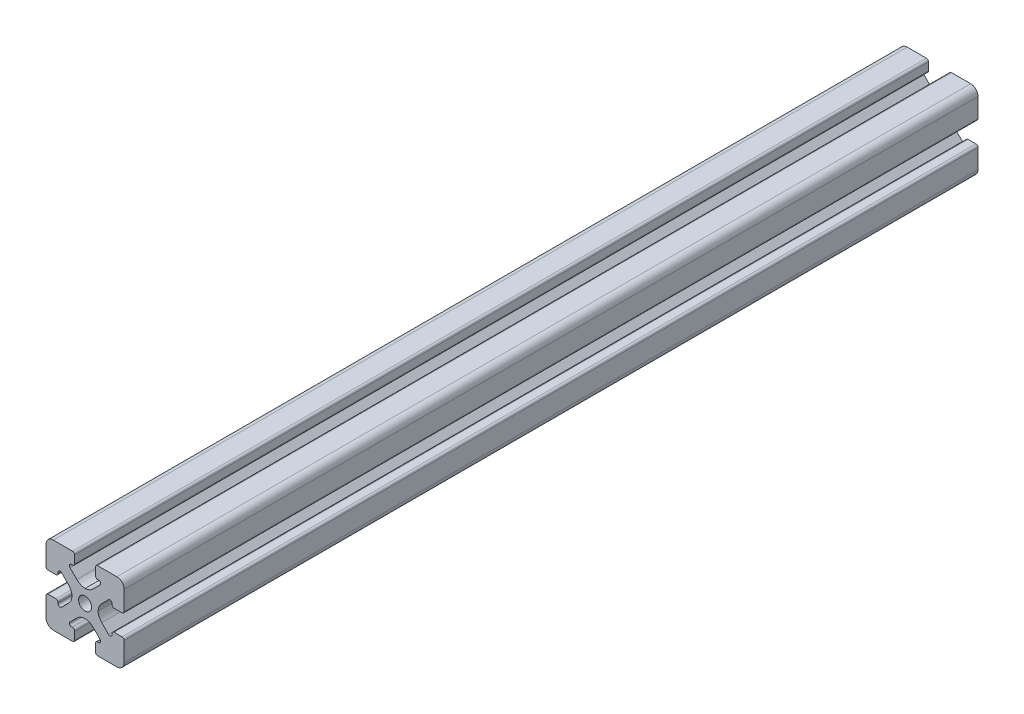
SolidWorks part; units mm, degrees
ref_plane "Front Plane" through (0, 0, 0) normal (0, 0, 1) x (1, 0, 0)
ref_plane "Top Plane" through (0, 0, 0) normal (0, 1, 0) x (1, 0, 0)
ref_plane "Right Plane" through (0, 0, 0) normal (1, 0, 0) x (0, 0, -1)
sketch "Sketch2" plane through (0, 0, 0) normal (0, 0, 1) x (1, 0, 0)
  line L0 (0, 7.5) -> (0, -7.5) construction
  line L1 (-7.5, 0) -> (7.5, 0) construction
  line L2 (2, -7.5) -> (7.5, -7.5)
  line L3 (7.5, -7.5) -> (7.5, -2)
  line L4 (2, -7.5) -> (2, -5.1953)
  line L5 (2, -5.1953) -> (3.5657, -5.1953)
  line L6 (3.5657, -5.1953) -> (0.8704, -2.5)
  line L7 (0, 0) -> (7.5, -7.5) construction
  line L8 (7.5, -2) -> (5.1953, -2)
  line L9 (5.1953, -2) -> (5.1953, -3.5657)
  line L10 (5.1953, -3.5657) -> (2.5, -0.8704)
  line L11 (3.8477, -2.218) -> (2.218, -3.8477) construction
  circle A0 centre (0, 0) radius 1.25
  arc A1 (2.6, -5.1953) -> (2.8828, -4.5125) centre (2.6, -4.7953) ccw construction
  point P8 (0, -2.5)
  point P16 (3.0328, -3.0328)
  dimension "Center Hole Diameter" = 2.5
  dimension "D3" = 0.4
  dimension "Rail Height" = 15
  dimension "Rail Width" = 15
  dimension "T-Slot Width" = 4
  dimension "Slot Depth" = 5
  dimension "Slot Inner Width" = 6
sketch "Sketch3" plane through (0, 0, 0) normal (1, 0, 0) x (0, 0, -1)
  line L0 (-82, -7.5) -> (82, -7.5) construction
  line L1 (-56.6, 0) -> (56.6, 0) construction
  line L2 (0, 7.5) -> (0, -7.5) construction
  line L3 (0, 7.5) -> (0, -7.5) construction
  point P6 (-56.6, 0)
  point P8 (56.6, 0)
  dimension "Length" = 164
  dimension "D1" = 25.4
sketch "Sketch4" plane through (0, 0, 0) normal (0, 0, 1) x (1, 0, 0)
  line L0 (2.4, -7.5) -> (6.1, -7.5)
  line L1 (2, -7.5) -> (7.5, -7.5) construction
  line L2 (2, -7.5) -> (2, -5.1953) construction
  line L3 (2, -5.1953) -> (3.5657, -5.1953) construction
  line L4 (2, -5.5953) -> (2, -7.1)
  line L5 (2.4, -5.1953) -> (2.6, -5.1953)
  line L6 (0, -2.5) -> (-0.1238, -2.5)
  line L7 (3.5657, -5.1953) -> (0.8704, -2.5) construction
  line L8 (1.5733, -3.2029) -> (2.8828, -4.5125)
  line L9 (7.5, -7.5) -> (7.5, -2) construction
  line L10 (5.1953, -3.5657) -> (2.5, -0.8704) construction
  line L11 (5.1953, -2) -> (5.1953, -3.5657) construction
  line L12 (5.1953, -2.6) -> (5.1953, -2.4)
  line L13 (7.5, -2) -> (5.1953, -2) construction
  line L14 (5.5953, -2) -> (7.1, -2)
  line L15 (7.5, -2.4) -> (7.5, -6.1)
  line L16 (4.5125, -2.8828) -> (3.2029, -1.5733)
  line L17 (2.5, 0) -> (2.5, 0.1238)
  line L18 (-7.5, 0) -> (7.5, 0) construction
  line L19 (0, -2.5) -> (0, -1.25)
  line L20 (0, 7.5) -> (0, -7.5) construction
  line L21 (2.5, 0) -> (1.25, 0)
  arc A0 (2, -7.1) -> (2.4, -7.5) centre (2.4, -7.1) ccw
  arc A1 (2.6, -5.1953) -> (2.8828, -4.5125) centre (2.6, -4.7953) ccw construction
  arc A2 (2, -5.5953) -> (2.4, -5.1953) centre (2.4, -5.5953) cw
  arc A3 (2.6, -5.1953) -> (2.8828, -4.5125) centre (2.6, -4.7953) ccw
  arc A4 (-0.1238, -2.5) -> (1.5733, -3.2029) centre (-0.1238, -4.9) cw
  arc A5 (6.1, -7.5) -> (7.5, -6.1) centre (6.1, -6.1) ccw
  arc A6 (4.5125, -2.8828) -> (5.1953, -2.6) centre (4.7953, -2.6) ccw
  arc A7 (5.1953, -2.4) -> (5.5953, -2) centre (5.5953, -2.4) cw
  arc A8 (7.1, -2) -> (7.5, -2.4) centre (7.1, -2.4) cw
  arc A9 (3.2029, -1.5733) -> (2.5, 0.1238) centre (4.9, 0.1238) cw
  circle A10 centre (0, 0) radius 1.25 construction
  arc A11 (0, -1.25) -> (1.25, 0) centre (0, 0) ccw
  dimension "D1" = 1.4
  dimension "D2" = 2.4
extrude "Boss-Extrude1" add sketch "Sketch4" along normal mid plane 164
mirror "Mirror1" about plane through (0, 0, 0) normal (1, 0, 0) of bodies 134
mirror "Mirror2" about plane through (0, 0, 0) normal (0, 1, 0) of bodies 135
equation "\"D3@Sketch2\"=\"T-Slot Width@Sketch2\"*0.1"
equation "\"D1@Sketch4\"=\"D3@Sketch2\"*3.5"
equation "\"D2@Sketch4\"=\"D3@Sketch2\"*6"
equation "\"D1@Boss-Extrude1\"=\"Length@Sketch3\""
